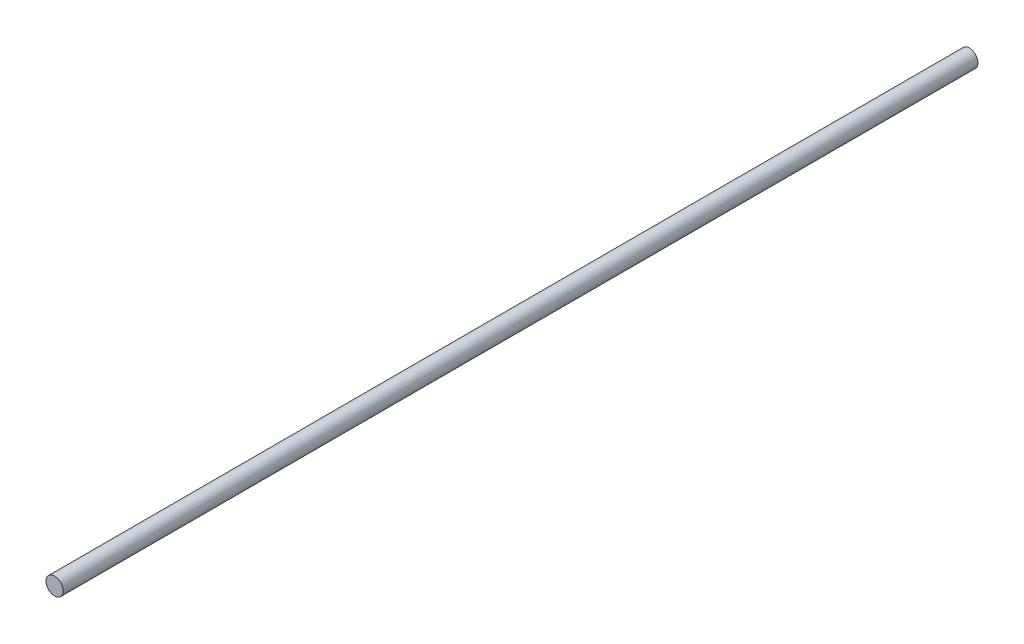
SolidWorks part; units mm, degrees
ref_plane "Front Plane" through (0, 0, 0) normal (0, 0, 1) x (1, 0, 0)
ref_plane "Top Plane" through (0, 0, 0) normal (0, 1, 0) x (1, 0, 0)
ref_plane "Right Plane" through (0, 0, 0) normal (1, 0, 0) x (0, 0, -1)
sketch "Sketch1" plane through (0, 0, 0) normal (0, 0, 1) x (1, 0, 0)
  circle A0 centre (0, 0) radius 4
extrude "Boss-Extrude1" add sketch "Sketch1" along normal blind 425
